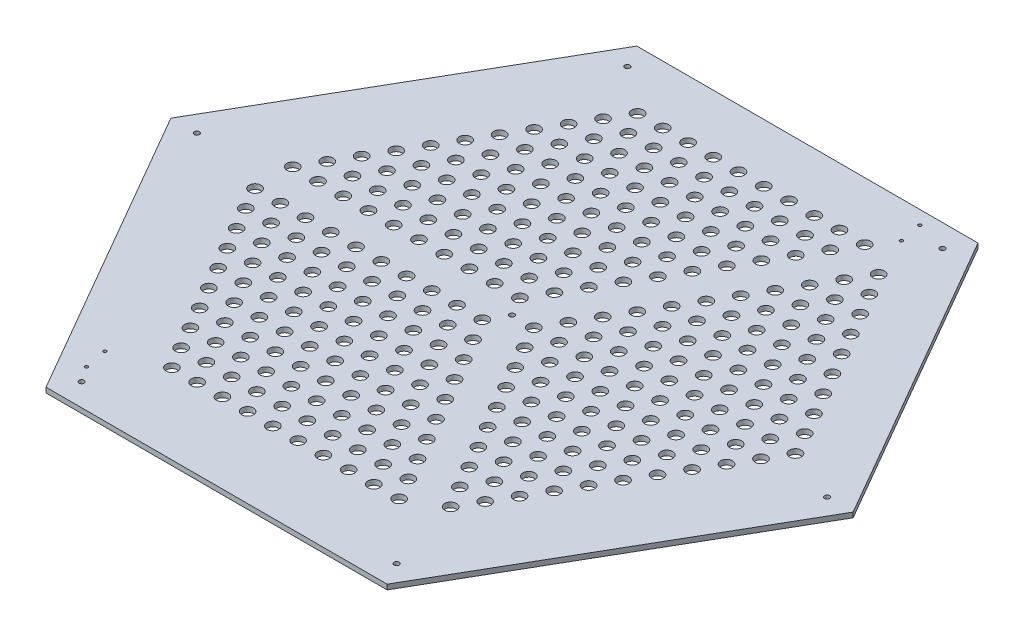
SolidWorks part; units mm, degrees
material "Oak"
ref_plane "Front Plane" through (0, 0, 0) normal (0, 0, 1) x (1, 0, 0)
ref_plane "Top Plane" through (0, 0, 0) normal (0, 1, 0) x (1, 0, 0)
ref_plane "Right Plane" through (0, 0, 0) normal (1, 0, 0) x (0, 0, -1)
sketch "Sketch1" plane through (0, 0, 0) normal (0, 1, 0) x (1, 0, 0)
  line L1 (433.0127, 0) -> (216.5064, 375)
  line L2 (216.5064, 375) -> (-216.5064, 375)
  line L3 (-216.5064, 375) -> (-433.0127, 0)
  line L4 (-433.0127, 0) -> (-216.5064, -375)
  line L5 (-216.5064, -375) -> (216.5064, -375)
  line L6 (216.5064, -375) -> (433.0127, 0)
  circle A1 centre (0, 0) radius 375 construction
extrude "Base" add sketch "Sketch1" along normal blind 6.35
sketch "Border Sketch" plane through (0, 6.35, 0) normal (0, 1, 0) x (1, 0, 0)
  line L7 (450, 0) -> (225, 389.7114)
  line L8 (225, 389.7114) -> (-225, 389.7114)
  line L9 (-225, 389.7114) -> (-450, 0)
  line L10 (-450, 0) -> (-225, -389.7114)
  line L11 (-225, -389.7114) -> (225, -389.7114)
  line L12 (225, -389.7114) -> (450, 0)
  line L14 (225, 389.7114) -> (0, 0)
  line L15 (0, 0) -> (225, -389.7114)
  line L20 (-450, 0) -> (0, 0)
  line L21 (0, 5.5) -> (-446.8246, 5.5)
  line L22 (0, -5.5) -> (-446.8246, -5.5)
  line L23 (218.6491, 389.7114) -> (-4.7631, 2.75)
  line L24 (4.7631, -2.75) -> (228.1754, 384.2114)
  line L25 (4.7631, 2.75) -> (228.1754, -384.2114)
  line L26 (-4.7631, -2.75) -> (218.6491, -389.7114)
  circle A0 centre (0, 0) radius 450 construction
  circle A1 centre (0, 0) radius 5.5
  dimension "D1" = 5.5
  dimension "D2" = 5.5
  dimension "D3" = 5.5
  dimension "D4" = 5.5
sketch "Sketch3" plane through (0, 6.35, 0) normal (0, 1, 0) x (1, 0, 0)
  circle A1 centre (27.6379, 0.0396) radius 7.5
  circle A2 centre (43.6579, 27.787) radius 7.5
  circle A3 centre (59.6779, 55.5345) radius 7.5
  circle A4 centre (75.6979, 83.2819) radius 7.5
  circle A5 centre (91.7179, 111.0294) radius 7.5
  circle A6 centre (107.7379, 138.7768) radius 7.5
  circle A7 centre (123.7579, 166.5243) radius 7.5
  circle A8 centre (139.7779, 194.2717) radius 7.5
  circle A9 centre (155.7979, 222.0192) radius 7.5
  circle A10 centre (171.8179, 249.7666) radius 7.5
  circle A11 centre (187.8379, 277.5141) radius 7.5
  circle A12 centre (59.6779, 0.0396) radius 7.5
  circle A13 centre (75.6979, 27.787) radius 7.5
  circle A14 centre (91.7179, 55.5345) radius 7.5
  circle A15 centre (107.7379, 83.2819) radius 7.5
  circle A16 centre (123.7579, 111.0294) radius 7.5
  circle A17 centre (139.7779, 138.7768) radius 7.5
  circle A18 centre (155.7979, 166.5243) radius 7.5
  circle A19 centre (171.8179, 194.2717) radius 7.5
  circle A20 centre (187.8379, 222.0192) radius 7.5
  circle A21 centre (203.8579, 249.7666) radius 7.5
  circle A22 centre (75.6979, -27.7079) radius 7.5
  circle A23 centre (91.7179, 0.0396) radius 7.5
  circle A24 centre (107.7379, 27.787) radius 7.5
  circle A25 centre (123.7579, 55.5345) radius 7.5
  circle A26 centre (139.7779, 83.2819) radius 7.5
  circle A27 centre (155.7979, 111.0294) radius 7.5
  circle A28 centre (171.8179, 138.7768) radius 7.5
  circle A29 centre (187.8379, 166.5243) radius 7.5
  circle A30 centre (203.8579, 194.2717) radius 7.5
  circle A31 centre (219.8779, 222.0192) radius 7.5
  circle A32 centre (91.7179, -55.4553) radius 7.5
  circle A33 centre (107.7379, -27.7079) radius 7.5
  circle A34 centre (123.7579, 0.0396) radius 7.5
  circle A35 centre (139.7779, 27.787) radius 7.5
  circle A36 centre (155.7979, 55.5345) radius 7.5
  circle A37 centre (171.8179, 83.2819) radius 7.5
  circle A38 centre (187.8379, 111.0294) radius 7.5
  circle A39 centre (203.8579, 138.7768) radius 7.5
  circle A40 centre (219.8779, 166.5243) radius 7.5
  circle A41 centre (235.8979, 194.2717) radius 7.5
  circle A42 centre (107.7379, -83.2028) radius 7.5
  circle A43 centre (123.7579, -55.4553) radius 7.5
  circle A44 centre (139.7779, -27.7079) radius 7.5
  circle A45 centre (155.7979, 0.0396) radius 7.5
  circle A46 centre (171.8179, 27.787) radius 7.5
  circle A47 centre (187.8379, 55.5345) radius 7.5
  circle A48 centre (203.8579, 83.2819) radius 7.5
  circle A49 centre (219.8779, 111.0294) radius 7.5
  circle A50 centre (235.8979, 138.7768) radius 7.5
  circle A51 centre (251.9179, 166.5243) radius 7.5
  circle A52 centre (123.7579, -110.9503) radius 7.5
  circle A53 centre (139.7779, -83.2028) radius 7.5
  circle A54 centre (155.7979, -55.4553) radius 7.5
  circle A55 centre (171.8179, -27.7079) radius 7.5
  circle A56 centre (187.8379, 0.0396) radius 7.5
  circle A57 centre (203.8579, 27.787) radius 7.5
  circle A58 centre (219.8779, 55.5345) radius 7.5
  circle A59 centre (235.8979, 83.2819) radius 7.5
  circle A60 centre (251.9179, 111.0294) radius 7.5
  circle A61 centre (267.9379, 138.7768) radius 7.5
  circle A62 centre (139.7779, -138.6977) radius 7.5
  circle A63 centre (155.7979, -110.9503) radius 7.5
  circle A64 centre (171.8179, -83.2028) radius 7.5
  circle A65 centre (187.8379, -55.4553) radius 7.5
  circle A66 centre (203.8579, -27.7079) radius 7.5
  circle A67 centre (219.8779, 0.0396) radius 7.5
  circle A68 centre (235.8979, 27.787) radius 7.5
  circle A69 centre (251.9179, 55.5345) radius 7.5
  circle A70 centre (267.9379, 83.2819) radius 7.5
  circle A71 centre (283.9579, 111.0294) radius 7.5
  circle A72 centre (155.7979, -166.4452) radius 7.5
  circle A73 centre (171.8179, -138.6977) radius 7.5
  circle A74 centre (187.8379, -110.9503) radius 7.5
  circle A75 centre (203.8579, -83.2028) radius 7.5
  circle A76 centre (219.8779, -55.4553) radius 7.5
  circle A77 centre (235.8979, -27.7079) radius 7.5
  circle A78 centre (251.9179, 0.0396) radius 7.5
  circle A79 centre (267.9379, 27.787) radius 7.5
  circle A80 centre (283.9579, 55.5345) radius 7.5
  circle A81 centre (299.9779, 83.2819) radius 7.5
  circle A82 centre (171.8179, -194.1926) radius 7.5
  circle A83 centre (187.8379, -166.4452) radius 7.5
  circle A84 centre (203.8579, -138.6977) radius 7.5
  circle A85 centre (219.8779, -110.9503) radius 7.5
  circle A86 centre (235.8979, -83.2028) radius 7.5
  circle A87 centre (251.9179, -55.4553) radius 7.5
  circle A88 centre (267.9379, -27.7079) radius 7.5
  circle A89 centre (283.9579, 0.0396) radius 7.5
  circle A90 centre (299.9779, 27.787) radius 7.5
  circle A91 centre (315.9979, 55.5345) radius 7.5
  circle A92 centre (187.8379, -221.9401) radius 7.5
  circle A93 centre (203.8579, -194.1926) radius 7.5
  circle A94 centre (219.8779, -166.4452) radius 7.5
  circle A95 centre (235.8979, -138.6977) radius 7.5
  circle A96 centre (251.9179, -110.9503) radius 7.5
  circle A97 centre (267.9379, -83.2028) radius 7.5
  circle A98 centre (283.9579, -55.4553) radius 7.5
  circle A99 centre (299.9779, -27.7079) radius 7.5
  circle A100 centre (315.9979, 0.0396) radius 7.5
  circle A101 centre (332.0179, 27.787) radius 7.5
  circle A102 centre (43.6579, -27.7079) radius 7.5
  circle A103 centre (59.6779, -55.4553) radius 7.5
  circle A104 centre (75.6979, -83.2028) radius 7.5
  circle A105 centre (91.7179, -110.9503) radius 7.5
  circle A106 centre (107.7379, -138.6977) radius 7.5
  circle A107 centre (123.7579, -166.4452) radius 7.5
  circle A108 centre (139.7779, -194.1926) radius 7.5
  circle A109 centre (155.7979, -221.9401) radius 7.5
  circle A110 centre (171.8179, -249.6875) radius 7.5
  circle A111 centre (-13.8596, -23.9117) radius 7.5
  circle A112 centre (-45.8996, -23.9117) radius 7.5
  circle A113 centre (-77.9396, -23.9117) radius 7.5
  circle A114 centre (-109.9796, -23.9117) radius 7.5
  circle A115 centre (-142.0196, -23.9117) radius 7.5
  circle A116 centre (-174.0596, -23.9117) radius 7.5
  circle A117 centre (-206.0996, -23.9117) radius 7.5
  circle A118 centre (-238.1396, -23.9117) radius 7.5
  circle A119 centre (-270.1796, -23.9117) radius 7.5
  circle A120 centre (-302.2196, -23.9117) radius 7.5
  circle A121 centre (-29.8796, -51.6591) radius 7.5
  circle A122 centre (-61.9196, -51.6591) radius 7.5
  circle A123 centre (-93.9596, -51.6591) radius 7.5
  circle A124 centre (-125.9996, -51.6591) radius 7.5
  circle A125 centre (-158.0396, -51.6591) radius 7.5
  circle A126 centre (-190.0796, -51.6591) radius 7.5
  circle A127 centre (-222.1196, -51.6591) radius 7.5
  circle A128 centre (-254.1596, -51.6591) radius 7.5
  circle A129 centre (-286.1996, -51.6591) radius 7.5
  circle A130 centre (-13.8596, -79.4066) radius 7.5
  circle A131 centre (-45.8996, -79.4066) radius 7.5
  circle A132 centre (-77.9396, -79.4066) radius 7.5
  circle A133 centre (-109.9796, -79.4066) radius 7.5
  circle A134 centre (-142.0196, -79.4066) radius 7.5
  circle A135 centre (-174.0596, -79.4066) radius 7.5
  circle A136 centre (-206.0996, -79.4066) radius 7.5
  circle A137 centre (-238.1396, -79.4066) radius 7.5
  circle A138 centre (-270.1796, -79.4066) radius 7.5
  circle A139 centre (2.1604, -107.154) radius 7.5
  circle A140 centre (-29.8796, -107.154) radius 7.5
  circle A141 centre (-61.9196, -107.154) radius 7.5
  circle A142 centre (-93.9596, -107.154) radius 7.5
  circle A143 centre (-125.9996, -107.154) radius 7.5
  circle A144 centre (-158.0396, -107.154) radius 7.5
  circle A145 centre (-190.0796, -107.154) radius 7.5
  circle A146 centre (-222.1196, -107.154) radius 7.5
  circle A147 centre (-254.1596, -107.154) radius 7.5
  circle A148 centre (18.1804, -134.9015) radius 7.5
  circle A149 centre (-13.8596, -134.9015) radius 7.5
  circle A150 centre (-45.8996, -134.9015) radius 7.5
  circle A151 centre (-77.9396, -134.9015) radius 7.5
  circle A152 centre (-109.9796, -134.9015) radius 7.5
  circle A153 centre (-142.0196, -134.9015) radius 7.5
  circle A154 centre (-174.0596, -134.9015) radius 7.5
  circle A155 centre (-206.0996, -134.9015) radius 7.5
  circle A156 centre (-238.1396, -134.9015) radius 7.5
  circle A157 centre (34.2004, -162.649) radius 7.5
  circle A158 centre (2.1604, -162.649) radius 7.5
  circle A159 centre (-29.8796, -162.649) radius 7.5
  circle A160 centre (-61.9196, -162.649) radius 7.5
  circle A161 centre (-93.9596, -162.649) radius 7.5
  circle A162 centre (-125.9996, -162.649) radius 7.5
  circle A163 centre (-158.0396, -162.649) radius 7.5
  circle A164 centre (-190.0796, -162.649) radius 7.5
  circle A165 centre (-222.1196, -162.649) radius 7.5
  circle A166 centre (50.2204, -190.3964) radius 7.5
  circle A167 centre (18.1804, -190.3964) radius 7.5
  circle A168 centre (-13.8596, -190.3964) radius 7.5
  circle A169 centre (-45.8996, -190.3964) radius 7.5
  circle A170 centre (-77.9396, -190.3964) radius 7.5
  circle A171 centre (-109.9796, -190.3964) radius 7.5
  circle A172 centre (-142.0196, -190.3964) radius 7.5
  circle A173 centre (-174.0596, -190.3964) radius 7.5
  circle A174 centre (-206.0996, -190.3964) radius 7.5
  circle A175 centre (66.2404, -218.1439) radius 7.5
  circle A176 centre (34.2004, -218.1439) radius 7.5
  circle A177 centre (2.1604, -218.1439) radius 7.5
  circle A178 centre (-29.8796, -218.1439) radius 7.5
  circle A179 centre (-61.9196, -218.1439) radius 7.5
  circle A180 centre (-93.9596, -218.1439) radius 7.5
  circle A181 centre (-125.9996, -218.1439) radius 7.5
  circle A182 centre (-158.0396, -218.1439) radius 7.5
  circle A183 centre (-190.0796, -218.1439) radius 7.5
  circle A184 centre (82.2604, -245.8913) radius 7.5
  circle A185 centre (50.2204, -245.8913) radius 7.5
  circle A186 centre (18.1804, -245.8913) radius 7.5
  circle A187 centre (-13.8596, -245.8913) radius 7.5
  circle A188 centre (-45.8996, -245.8913) radius 7.5
  circle A189 centre (-77.9396, -245.8913) radius 7.5
  circle A190 centre (-109.9796, -245.8913) radius 7.5
  circle A191 centre (-142.0196, -245.8913) radius 7.5
  circle A192 centre (-174.0596, -245.8913) radius 7.5
  circle A193 centre (98.2804, -273.6388) radius 7.5
  circle A194 centre (66.2404, -273.6388) radius 7.5
  circle A195 centre (34.2004, -273.6388) radius 7.5
  circle A196 centre (2.1604, -273.6388) radius 7.5
  circle A197 centre (-29.8796, -273.6388) radius 7.5
  circle A198 centre (-61.9196, -273.6388) radius 7.5
  circle A199 centre (-93.9596, -273.6388) radius 7.5
  circle A200 centre (-125.9996, -273.6388) radius 7.5
  circle A201 centre (-158.0396, -273.6388) radius 7.5
  circle A202 centre (2.1604, -51.6591) radius 7.5
  circle A203 centre (18.1804, -79.4066) radius 7.5
  circle A204 centre (34.2004, -107.154) radius 7.5
  circle A205 centre (50.2204, -134.9015) radius 7.5
  circle A206 centre (66.2404, -162.649) radius 7.5
  circle A207 centre (82.2604, -190.3964) radius 7.5
  circle A208 centre (98.2804, -218.1439) radius 7.5
  circle A209 centre (114.3004, -245.8913) radius 7.5
  circle A210 centre (130.3204, -273.6388) radius 7.5
  circle A211 centre (-13.8532, 23.9154) radius 7.5
  circle A212 centre (2.1668, 51.6628) radius 7.5
  circle A213 centre (18.1868, 79.4103) radius 7.5
  circle A214 centre (34.2068, 107.1577) radius 7.5
  circle A215 centre (50.2268, 134.9052) radius 7.5
  circle A216 centre (66.2468, 162.6526) radius 7.5
  circle A217 centre (82.2668, 190.4001) radius 7.5
  circle A218 centre (98.2868, 218.1475) radius 7.5
  circle A219 centre (114.3068, 245.895) radius 7.5
  circle A220 centre (130.3268, 273.6425) radius 7.5
  circle A221 centre (146.3468, 301.3899) radius 7.5
  circle A222 centre (-29.8732, 51.6628) radius 7.5
  circle A223 centre (-13.8532, 79.4103) radius 7.5
  circle A224 centre (2.1668, 107.1577) radius 7.5
  circle A225 centre (18.1868, 134.9052) radius 7.5
  circle A226 centre (34.2068, 162.6526) radius 7.5
  circle A227 centre (50.2268, 190.4001) radius 7.5
  circle A228 centre (66.2468, 218.1475) radius 7.5
  circle A229 centre (82.2668, 245.895) radius 7.5
  circle A230 centre (98.2868, 273.6425) radius 7.5
  circle A231 centre (114.3068, 301.3899) radius 7.5
  circle A232 centre (-61.9132, 51.6628) radius 7.5
  circle A233 centre (-45.8932, 79.4103) radius 7.5
  circle A234 centre (-29.8732, 107.1577) radius 7.5
  circle A235 centre (-13.8532, 134.9052) radius 7.5
  circle A236 centre (2.1668, 162.6526) radius 7.5
  circle A237 centre (18.1868, 190.4001) radius 7.5
  circle A238 centre (34.2068, 218.1475) radius 7.5
  circle A239 centre (50.2268, 245.895) radius 7.5
  circle A240 centre (66.2468, 273.6425) radius 7.5
  circle A241 centre (82.2668, 301.3899) radius 7.5
  circle A242 centre (-93.9532, 51.6628) radius 7.5
  circle A243 centre (-77.9332, 79.4103) radius 7.5
  circle A244 centre (-61.9132, 107.1577) radius 7.5
  circle A245 centre (-45.8932, 134.9052) radius 7.5
  circle A246 centre (-29.8732, 162.6526) radius 7.5
  circle A247 centre (-13.8532, 190.4001) radius 7.5
  circle A248 centre (2.1668, 218.1475) radius 7.5
  circle A249 centre (18.1868, 245.895) radius 7.5
  circle A250 centre (34.2068, 273.6425) radius 7.5
  circle A251 centre (50.2268, 301.3899) radius 7.5
  circle A252 centre (-125.9932, 51.6628) radius 7.5
  circle A253 centre (-109.9732, 79.4103) radius 7.5
  circle A254 centre (-93.9532, 107.1577) radius 7.5
  circle A255 centre (-77.9332, 134.9052) radius 7.5
  circle A256 centre (-61.9132, 162.6526) radius 7.5
  circle A257 centre (-45.8932, 190.4001) radius 7.5
  circle A258 centre (-29.8732, 218.1475) radius 7.5
  circle A259 centre (-13.8532, 245.895) radius 7.5
  circle A260 centre (2.1668, 273.6425) radius 7.5
  circle A261 centre (18.1868, 301.3899) radius 7.5
  circle A262 centre (-158.0332, 51.6628) radius 7.5
  circle A263 centre (-142.0132, 79.4103) radius 7.5
  circle A264 centre (-125.9932, 107.1577) radius 7.5
  circle A265 centre (-109.9732, 134.9052) radius 7.5
  circle A266 centre (-93.9532, 162.6526) radius 7.5
  circle A267 centre (-77.9332, 190.4001) radius 7.5
  circle A268 centre (-61.9132, 218.1475) radius 7.5
  circle A269 centre (-45.8932, 245.895) radius 7.5
  circle A270 centre (-29.8732, 273.6425) radius 7.5
  circle A271 centre (-13.8532, 301.3899) radius 7.5
  circle A272 centre (-190.0732, 51.6628) radius 7.5
  circle A273 centre (-174.0532, 79.4103) radius 7.5
  circle A274 centre (-158.0332, 107.1577) radius 7.5
  circle A275 centre (-142.0132, 134.9052) radius 7.5
  circle A276 centre (-125.9932, 162.6526) radius 7.5
  circle A277 centre (-109.9732, 190.4001) radius 7.5
  circle A278 centre (-93.9532, 218.1475) radius 7.5
  circle A279 centre (-77.9332, 245.895) radius 7.5
  circle A280 centre (-61.9132, 273.6425) radius 7.5
  circle A281 centre (-45.8932, 301.3899) radius 7.5
  circle A282 centre (-222.1132, 51.6628) radius 7.5
  circle A283 centre (-206.0932, 79.4103) radius 7.5
  circle A284 centre (-190.0732, 107.1577) radius 7.5
  circle A285 centre (-174.0532, 134.9052) radius 7.5
  circle A286 centre (-158.0332, 162.6526) radius 7.5
  circle A287 centre (-142.0132, 190.4001) radius 7.5
  circle A288 centre (-125.9932, 218.1475) radius 7.5
  circle A289 centre (-109.9732, 245.895) radius 7.5
  circle A290 centre (-93.9532, 273.6425) radius 7.5
  circle A291 centre (-77.9332, 301.3899) radius 7.5
  circle A292 centre (-254.1532, 51.6628) radius 7.5
  circle A293 centre (-238.1332, 79.4103) radius 7.5
  circle A294 centre (-222.1132, 107.1577) radius 7.5
  circle A295 centre (-206.0932, 134.9052) radius 7.5
  circle A296 centre (-190.0732, 162.6526) radius 7.5
  circle A297 centre (-174.0532, 190.4001) radius 7.5
  circle A298 centre (-158.0332, 218.1475) radius 7.5
  circle A299 centre (-142.0132, 245.895) radius 7.5
  circle A300 centre (-125.9932, 273.6425) radius 7.5
  circle A301 centre (-109.9732, 301.3899) radius 7.5
  circle A302 centre (-286.1932, 51.6628) radius 7.5
  circle A303 centre (-270.1732, 79.4103) radius 7.5
  circle A304 centre (-254.1532, 107.1577) radius 7.5
  circle A305 centre (-238.1332, 134.9052) radius 7.5
  circle A306 centre (-222.1132, 162.6526) radius 7.5
  circle A307 centre (-206.0932, 190.4001) radius 7.5
  circle A308 centre (-190.0732, 218.1475) radius 7.5
  circle A309 centre (-174.0532, 245.895) radius 7.5
  circle A310 centre (-158.0332, 273.6425) radius 7.5
  circle A311 centre (-142.0132, 301.3899) radius 7.5
  circle A312 centre (-45.8932, 23.9154) radius 7.5
  circle A313 centre (-77.9332, 23.9154) radius 7.5
  circle A314 centre (-109.9732, 23.9154) radius 7.5
  circle A315 centre (-142.0132, 23.9154) radius 7.5
  circle A316 centre (-174.0532, 23.9154) radius 7.5
  circle A317 centre (-206.0932, 23.9154) radius 7.5
  circle A318 centre (-238.1332, 23.9154) radius 7.5
  circle A319 centre (-270.1732, 23.9154) radius 7.5
  circle A320 centre (-302.2132, 23.9154) radius 7.5
  dimension "D1" = 11
  dimension "D3" = 10
  dimension "D5" = 11
  dimension "D2" = 10
  dimension "D4" = 10
  dimension "D6" = 10
extrude "Cut-Extrude1" cut sketch "Sketch3" against normal up to next (6.35 mm away)
hole_wizard "Ø6.5 (6.5) Diameter Hole1" positions "Sketch4" profile "Sketch5" hole size "Ø6.5" standard "ANSI Metric"
sketch "Sketch4" plane through (0, 14.2875, 0) normal (0, 1, 0) x (-0.5, 0, 0.866)
  point P0 (0, 0)
  point P3 (-400, 0)
  point P11 (-200, 346.4102)
  point P12 (200, 346.4102)
  point P13 (400, 0)
  point P14 (200, -346.4102)
  point P15 (-200, -346.4102)
  point P16 (0, 0)
sketch "Sketch5" plane through (0, 14.2875, 0) normal (1, 0, 0) x (0, 0, 1)
  line L0 (0, 0) -> (0, 14.2875)
  line L1 (0, 14.2875) -> (3.25, 14.2875)
  line L2 (3.25, 14.2875) -> (3.25, 0)
  line L3 (3.25, 0) -> (0, 0)
  line L4 (0, -6.35) -> (0, 107.95) construction
  dimension "Thru Hole Dia." = 6.5
  dimension "Thru Hole Depth" = 14.2875
hole_wizard "Ø4.0 (4) Diameter Hole1" positions "Sketch6" profile "Sketch7" hole size "Ø4.0" standard "ANSI Metric"
sketch "Sketch6" plane through (0, 0, 0) normal (0, -1, 0) x (0.5, 0, -0.866)
  point P0 (-389.7627, -21.2724)
  point P3 (-367.5377, -40.3224)
  point P6 (367.5377, -21.2724)
  point P9 (389.7627, -40.3224)
sketch "Sketch7" plane through (-213.3038, 0, 326.9082) normal (1, 0, 0) x (0, 0, -1)
  line L0 (0, 0) -> (0, 6.35)
  line L1 (0, 6.35) -> (2, 6.35)
  line L2 (2, 6.35) -> (2, 0)
  line L3 (2, 0) -> (0, 0)
  line L4 (0, -6.35) -> (0, 107.95) construction
  dimension "Thru Hole Dia." = 4
  dimension "Thru Hole Depth" = 6.35
